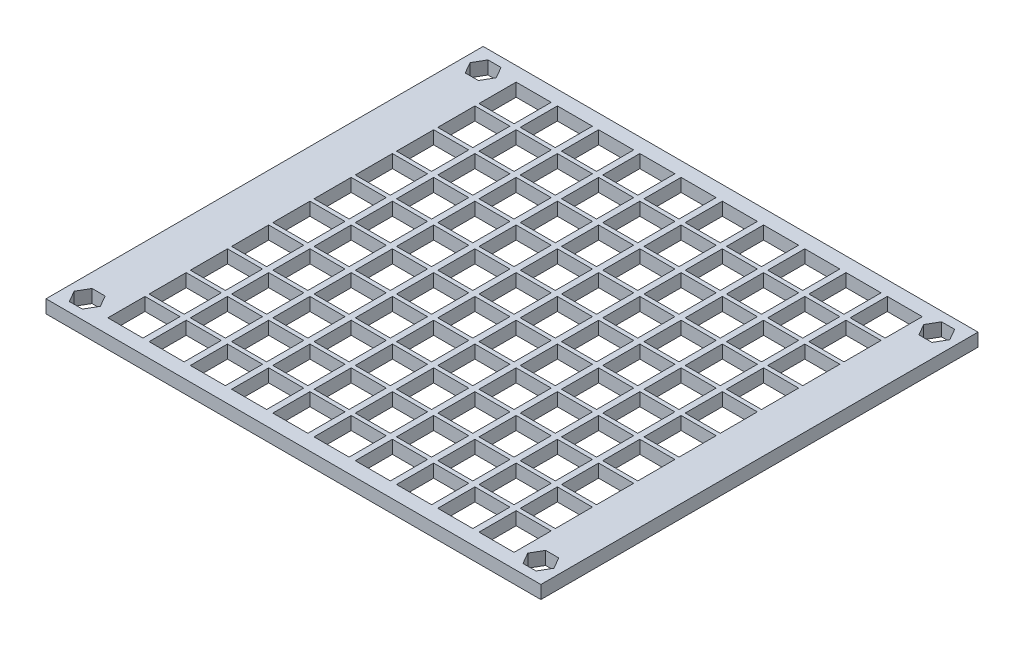
SolidWorks part; units mm, degrees
ref_plane "Front Plane" through (0, 0, 0) normal (0, 0, 1) x (1, 0, 0)
ref_plane "Top Plane" through (0, 0, 0) normal (0, 1, 0) x (1, 0, 0)
ref_plane "Right Plane" through (0, 0, 0) normal (1, 0, 0) x (0, 0, -1)
sketch "Sketch1" plane through (0, 0, 0) normal (0, 1, 0) x (1, 0, 0)
  line L0 (115, 101) -> (5, 101) construction
  line L1 (0, 0) -> (120, 0)
  line L2 (0, 0) -> (0, 106)
  line L3 (0, 106) -> (120, 106)
  line L4 (120, 0) -> (120, 106)
  line L6 (115, 101) -> (115, 5) construction
  line L8 (6.5877, 98.25) -> (8.1754, 101)
  line L9 (8.1754, 101) -> (6.5877, 103.75)
  line L10 (6.5877, 103.75) -> (3.4123, 103.75)
  line L11 (3.4123, 103.75) -> (1.8246, 101)
  line L12 (1.8246, 101) -> (3.4123, 98.25)
  line L13 (3.4123, 98.25) -> (6.5877, 98.25)
  line L14 (21.5, 12.5) -> (21.5, 3.5)
  line L15 (11.5, 12.5) -> (20, 12.5)
  line L16 (11.5, 12.5) -> (11.5, 3.5)
  line L17 (11.5, 3.5) -> (20, 3.5)
  line L18 (20, 12.5) -> (20, 3.5)
  line L19 (21.5, 12.5) -> (30, 12.5)
  line L20 (30, 12.5) -> (30, 3.5)
  line L21 (21.5, 3.5) -> (30, 3.5)
  line L22 (31.5, 12.5) -> (31.5, 3.5)
  line L23 (31.5, 12.5) -> (40, 12.5)
  line L24 (40, 12.5) -> (40, 3.5)
  line L25 (31.5, 3.5) -> (40, 3.5)
  line L26 (41.5, 12.5) -> (41.5, 3.5)
  line L27 (41.5, 12.5) -> (50, 12.5)
  line L28 (50, 12.5) -> (50, 3.5)
  line L29 (41.5, 3.5) -> (50, 3.5)
  line L30 (51.5, 12.5) -> (51.5, 3.5)
  line L31 (51.5, 12.5) -> (60, 12.5)
  line L32 (60, 12.5) -> (60, 3.5)
  line L33 (51.5, 3.5) -> (60, 3.5)
  line L34 (61.5, 12.5) -> (61.5, 3.5)
  line L35 (61.5, 12.5) -> (70, 12.5)
  line L36 (70, 12.5) -> (70, 3.5)
  line L37 (61.5, 3.5) -> (70, 3.5)
  line L38 (71.5, 12.5) -> (71.5, 3.5)
  line L39 (71.5, 12.5) -> (80, 12.5)
  line L40 (80, 12.5) -> (80, 3.5)
  line L41 (71.5, 3.5) -> (80, 3.5)
  line L42 (81.5, 12.5) -> (81.5, 3.5)
  line L43 (81.5, 12.5) -> (90, 12.5)
  line L44 (90, 12.5) -> (90, 3.5)
  line L45 (81.5, 3.5) -> (90, 3.5)
  line L46 (91.5, 12.5) -> (91.5, 3.5)
  line L47 (91.5, 12.5) -> (100, 12.5)
  line L48 (100, 12.5) -> (100, 3.5)
  line L49 (91.5, 3.5) -> (100, 3.5)
  line L50 (101.5, 12.5) -> (101.5, 3.5)
  line L51 (101.5, 12.5) -> (110, 12.5)
  line L52 (110, 12.5) -> (110, 3.5)
  line L53 (101.5, 3.5) -> (110, 3.5)
  line L54 (21.5, 22.5) -> (21.5, 13.5)
  line L55 (21.5, 22.5) -> (30, 22.5)
  line L56 (30, 22.5) -> (30, 13.5)
  line L57 (21.5, 13.5) -> (30, 13.5)
  line L58 (31.5, 22.5) -> (31.5, 13.5)
  line L59 (31.5, 22.5) -> (40, 22.5)
  line L60 (40, 22.5) -> (40, 13.5)
  line L61 (31.5, 13.5) -> (40, 13.5)
  line L62 (41.5, 22.5) -> (41.5, 13.5)
  line L63 (41.5, 22.5) -> (50, 22.5)
  line L64 (50, 22.5) -> (50, 13.5)
  line L65 (41.5, 13.5) -> (50, 13.5)
  line L66 (51.5, 22.5) -> (51.5, 13.5)
  line L67 (51.5, 22.5) -> (60, 22.5)
  line L68 (60, 22.5) -> (60, 13.5)
  line L69 (51.5, 13.5) -> (60, 13.5)
  line L70 (61.5, 22.5) -> (61.5, 13.5)
  line L71 (61.5, 22.5) -> (70, 22.5)
  line L72 (70, 22.5) -> (70, 13.5)
  line L73 (61.5, 13.5) -> (70, 13.5)
  line L74 (71.5, 22.5) -> (71.5, 13.5)
  line L75 (71.5, 22.5) -> (80, 22.5)
  line L76 (80, 22.5) -> (80, 13.5)
  line L77 (71.5, 13.5) -> (80, 13.5)
  line L78 (81.5, 22.5) -> (81.5, 13.5)
  line L79 (81.5, 22.5) -> (90, 22.5)
  line L80 (90, 22.5) -> (90, 13.5)
  line L81 (81.5, 13.5) -> (90, 13.5)
  line L82 (91.5, 22.5) -> (91.5, 13.5)
  line L83 (91.5, 22.5) -> (100, 22.5)
  line L84 (100, 22.5) -> (100, 13.5)
  line L85 (91.5, 13.5) -> (100, 13.5)
  line L86 (101.5, 22.5) -> (101.5, 13.5)
  line L87 (101.5, 22.5) -> (110, 22.5)
  line L88 (110, 22.5) -> (110, 13.5)
  line L89 (101.5, 13.5) -> (110, 13.5)
  line L90 (21.5, 32.5) -> (21.5, 23.5)
  line L91 (21.5, 32.5) -> (30, 32.5)
  line L92 (30, 32.5) -> (30, 23.5)
  line L93 (21.5, 23.5) -> (30, 23.5)
  line L94 (31.5, 32.5) -> (31.5, 23.5)
  line L95 (31.5, 32.5) -> (40, 32.5)
  line L96 (40, 32.5) -> (40, 23.5)
  line L97 (31.5, 23.5) -> (40, 23.5)
  line L98 (41.5, 32.5) -> (41.5, 23.5)
  line L99 (41.5, 32.5) -> (50, 32.5)
  line L100 (50, 32.5) -> (50, 23.5)
  line L101 (41.5, 23.5) -> (50, 23.5)
  line L102 (51.5, 32.5) -> (51.5, 23.5)
  line L103 (51.5, 32.5) -> (60, 32.5)
  line L104 (60, 32.5) -> (60, 23.5)
  line L105 (51.5, 23.5) -> (60, 23.5)
  line L106 (61.5, 32.5) -> (61.5, 23.5)
  line L107 (61.5, 32.5) -> (70, 32.5)
  line L108 (70, 32.5) -> (70, 23.5)
  line L109 (61.5, 23.5) -> (70, 23.5)
  line L110 (71.5, 32.5) -> (71.5, 23.5)
  line L111 (71.5, 32.5) -> (80, 32.5)
  line L112 (80, 32.5) -> (80, 23.5)
  line L113 (71.5, 23.5) -> (80, 23.5)
  line L114 (81.5, 32.5) -> (81.5, 23.5)
  line L115 (81.5, 32.5) -> (90, 32.5)
  line L116 (90, 32.5) -> (90, 23.5)
  line L117 (81.5, 23.5) -> (90, 23.5)
  line L118 (91.5, 32.5) -> (91.5, 23.5)
  line L119 (91.5, 32.5) -> (100, 32.5)
  line L120 (100, 32.5) -> (100, 23.5)
  line L121 (91.5, 23.5) -> (100, 23.5)
  line L122 (101.5, 32.5) -> (101.5, 23.5)
  line L123 (101.5, 32.5) -> (110, 32.5)
  line L124 (110, 32.5) -> (110, 23.5)
  line L125 (101.5, 23.5) -> (110, 23.5)
  line L126 (21.5, 42.5) -> (21.5, 33.5)
  line L127 (21.5, 42.5) -> (30, 42.5)
  line L128 (30, 42.5) -> (30, 33.5)
  line L129 (21.5, 33.5) -> (30, 33.5)
  line L130 (31.5, 42.5) -> (31.5, 33.5)
  line L131 (31.5, 42.5) -> (40, 42.5)
  line L132 (40, 42.5) -> (40, 33.5)
  line L133 (31.5, 33.5) -> (40, 33.5)
  line L134 (41.5, 42.5) -> (41.5, 33.5)
  line L135 (41.5, 42.5) -> (50, 42.5)
  line L136 (50, 42.5) -> (50, 33.5)
  line L137 (41.5, 33.5) -> (50, 33.5)
  line L138 (51.5, 42.5) -> (51.5, 33.5)
  line L139 (51.5, 42.5) -> (60, 42.5)
  line L140 (60, 42.5) -> (60, 33.5)
  line L141 (51.5, 33.5) -> (60, 33.5)
  line L142 (61.5, 42.5) -> (61.5, 33.5)
  line L143 (61.5, 42.5) -> (70, 42.5)
  line L144 (70, 42.5) -> (70, 33.5)
  line L145 (61.5, 33.5) -> (70, 33.5)
  line L146 (71.5, 42.5) -> (71.5, 33.5)
  line L147 (71.5, 42.5) -> (80, 42.5)
  line L148 (80, 42.5) -> (80, 33.5)
  line L149 (71.5, 33.5) -> (80, 33.5)
  line L150 (81.5, 42.5) -> (81.5, 33.5)
  line L151 (81.5, 42.5) -> (90, 42.5)
  line L152 (90, 42.5) -> (90, 33.5)
  line L153 (81.5, 33.5) -> (90, 33.5)
  line L154 (91.5, 42.5) -> (91.5, 33.5)
  line L155 (91.5, 42.5) -> (100, 42.5)
  line L156 (100, 42.5) -> (100, 33.5)
  line L157 (91.5, 33.5) -> (100, 33.5)
  line L158 (101.5, 42.5) -> (101.5, 33.5)
  line L159 (101.5, 42.5) -> (110, 42.5)
  line L160 (110, 42.5) -> (110, 33.5)
  line L161 (101.5, 33.5) -> (110, 33.5)
  line L162 (21.5, 52.5) -> (21.5, 43.5)
  line L163 (21.5, 52.5) -> (30, 52.5)
  line L164 (30, 52.5) -> (30, 43.5)
  line L165 (21.5, 43.5) -> (30, 43.5)
  line L166 (31.5, 52.5) -> (31.5, 43.5)
  line L167 (31.5, 52.5) -> (40, 52.5)
  line L168 (40, 52.5) -> (40, 43.5)
  line L169 (31.5, 43.5) -> (40, 43.5)
  line L170 (41.5, 52.5) -> (41.5, 43.5)
  line L171 (41.5, 52.5) -> (50, 52.5)
  line L172 (50, 52.5) -> (50, 43.5)
  line L173 (41.5, 43.5) -> (50, 43.5)
  line L174 (51.5, 52.5) -> (51.5, 43.5)
  line L175 (51.5, 52.5) -> (60, 52.5)
  line L176 (60, 52.5) -> (60, 43.5)
  line L177 (51.5, 43.5) -> (60, 43.5)
  line L178 (61.5, 52.5) -> (61.5, 43.5)
  line L179 (61.5, 52.5) -> (70, 52.5)
  line L180 (70, 52.5) -> (70, 43.5)
  line L181 (61.5, 43.5) -> (70, 43.5)
  line L182 (71.5, 52.5) -> (71.5, 43.5)
  line L183 (71.5, 52.5) -> (80, 52.5)
  line L184 (80, 52.5) -> (80, 43.5)
  line L185 (71.5, 43.5) -> (80, 43.5)
  line L186 (81.5, 52.5) -> (81.5, 43.5)
  line L187 (81.5, 52.5) -> (90, 52.5)
  line L188 (90, 52.5) -> (90, 43.5)
  line L189 (81.5, 43.5) -> (90, 43.5)
  line L190 (91.5, 52.5) -> (91.5, 43.5)
  line L191 (91.5, 52.5) -> (100, 52.5)
  line L192 (100, 52.5) -> (100, 43.5)
  line L193 (91.5, 43.5) -> (100, 43.5)
  line L194 (101.5, 52.5) -> (101.5, 43.5)
  line L195 (101.5, 52.5) -> (110, 52.5)
  line L196 (110, 52.5) -> (110, 43.5)
  line L197 (101.5, 43.5) -> (110, 43.5)
  line L198 (21.5, 62.5) -> (21.5, 53.5)
  line L199 (21.5, 62.5) -> (30, 62.5)
  line L200 (30, 62.5) -> (30, 53.5)
  line L201 (21.5, 53.5) -> (30, 53.5)
  line L202 (31.5, 62.5) -> (31.5, 53.5)
  line L203 (31.5, 62.5) -> (40, 62.5)
  line L204 (40, 62.5) -> (40, 53.5)
  line L205 (31.5, 53.5) -> (40, 53.5)
  line L206 (41.5, 62.5) -> (41.5, 53.5)
  line L207 (41.5, 62.5) -> (50, 62.5)
  line L208 (50, 62.5) -> (50, 53.5)
  line L209 (41.5, 53.5) -> (50, 53.5)
  line L210 (51.5, 62.5) -> (51.5, 53.5)
  line L211 (51.5, 62.5) -> (60, 62.5)
  line L212 (60, 62.5) -> (60, 53.5)
  line L213 (51.5, 53.5) -> (60, 53.5)
  line L214 (61.5, 62.5) -> (61.5, 53.5)
  line L215 (61.5, 62.5) -> (70, 62.5)
  line L216 (70, 62.5) -> (70, 53.5)
  line L217 (61.5, 53.5) -> (70, 53.5)
  line L218 (71.5, 62.5) -> (71.5, 53.5)
  line L219 (71.5, 62.5) -> (80, 62.5)
  line L220 (80, 62.5) -> (80, 53.5)
  line L221 (71.5, 53.5) -> (80, 53.5)
  line L222 (81.5, 62.5) -> (81.5, 53.5)
  line L223 (81.5, 62.5) -> (90, 62.5)
  line L224 (90, 62.5) -> (90, 53.5)
  line L225 (81.5, 53.5) -> (90, 53.5)
  line L226 (91.5, 62.5) -> (91.5, 53.5)
  line L227 (91.5, 62.5) -> (100, 62.5)
  line L228 (100, 62.5) -> (100, 53.5)
  line L229 (91.5, 53.5) -> (100, 53.5)
  line L230 (101.5, 62.5) -> (101.5, 53.5)
  line L231 (101.5, 62.5) -> (110, 62.5)
  line L232 (110, 62.5) -> (110, 53.5)
  line L233 (101.5, 53.5) -> (110, 53.5)
  line L234 (21.5, 72.5) -> (21.5, 63.5)
  line L235 (21.5, 72.5) -> (30, 72.5)
  line L236 (30, 72.5) -> (30, 63.5)
  line L237 (21.5, 63.5) -> (30, 63.5)
  line L238 (31.5, 72.5) -> (31.5, 63.5)
  line L239 (31.5, 72.5) -> (40, 72.5)
  line L240 (40, 72.5) -> (40, 63.5)
  line L241 (31.5, 63.5) -> (40, 63.5)
  line L242 (41.5, 72.5) -> (41.5, 63.5)
  line L243 (41.5, 72.5) -> (50, 72.5)
  line L244 (50, 72.5) -> (50, 63.5)
  line L245 (41.5, 63.5) -> (50, 63.5)
  line L246 (51.5, 72.5) -> (51.5, 63.5)
  line L247 (51.5, 72.5) -> (60, 72.5)
  line L248 (60, 72.5) -> (60, 63.5)
  line L249 (51.5, 63.5) -> (60, 63.5)
  line L250 (61.5, 72.5) -> (61.5, 63.5)
  line L251 (61.5, 72.5) -> (70, 72.5)
  line L252 (70, 72.5) -> (70, 63.5)
  line L253 (61.5, 63.5) -> (70, 63.5)
  line L254 (71.5, 72.5) -> (71.5, 63.5)
  line L255 (71.5, 72.5) -> (80, 72.5)
  line L256 (80, 72.5) -> (80, 63.5)
  line L257 (71.5, 63.5) -> (80, 63.5)
  line L258 (81.5, 72.5) -> (81.5, 63.5)
  line L259 (81.5, 72.5) -> (90, 72.5)
  line L260 (90, 72.5) -> (90, 63.5)
  line L261 (81.5, 63.5) -> (90, 63.5)
  line L262 (91.5, 72.5) -> (91.5, 63.5)
  line L263 (91.5, 72.5) -> (100, 72.5)
  line L264 (100, 72.5) -> (100, 63.5)
  line L265 (91.5, 63.5) -> (100, 63.5)
  line L266 (101.5, 72.5) -> (101.5, 63.5)
  line L267 (101.5, 72.5) -> (110, 72.5)
  line L268 (110, 72.5) -> (110, 63.5)
  line L269 (101.5, 63.5) -> (110, 63.5)
  line L270 (21.5, 82.5) -> (21.5, 73.5)
  line L271 (21.5, 82.5) -> (30, 82.5)
  line L272 (30, 82.5) -> (30, 73.5)
  line L273 (21.5, 73.5) -> (30, 73.5)
  line L274 (31.5, 82.5) -> (31.5, 73.5)
  line L275 (31.5, 82.5) -> (40, 82.5)
  line L276 (40, 82.5) -> (40, 73.5)
  line L277 (31.5, 73.5) -> (40, 73.5)
  line L278 (41.5, 82.5) -> (41.5, 73.5)
  line L279 (41.5, 82.5) -> (50, 82.5)
  line L280 (50, 82.5) -> (50, 73.5)
  line L281 (41.5, 73.5) -> (50, 73.5)
  line L282 (51.5, 82.5) -> (51.5, 73.5)
  line L283 (51.5, 82.5) -> (60, 82.5)
  line L284 (60, 82.5) -> (60, 73.5)
  line L285 (51.5, 73.5) -> (60, 73.5)
  line L286 (61.5, 82.5) -> (61.5, 73.5)
  line L287 (61.5, 82.5) -> (70, 82.5)
  line L288 (70, 82.5) -> (70, 73.5)
  line L289 (61.5, 73.5) -> (70, 73.5)
  line L290 (71.5, 82.5) -> (71.5, 73.5)
  line L291 (71.5, 82.5) -> (80, 82.5)
  line L292 (80, 82.5) -> (80, 73.5)
  line L293 (71.5, 73.5) -> (80, 73.5)
  line L294 (81.5, 82.5) -> (81.5, 73.5)
  line L295 (81.5, 82.5) -> (90, 82.5)
  line L296 (90, 82.5) -> (90, 73.5)
  line L297 (81.5, 73.5) -> (90, 73.5)
  line L298 (91.5, 82.5) -> (91.5, 73.5)
  line L299 (91.5, 82.5) -> (100, 82.5)
  line L300 (100, 82.5) -> (100, 73.5)
  line L301 (91.5, 73.5) -> (100, 73.5)
  line L302 (101.5, 82.5) -> (101.5, 73.5)
  line L303 (101.5, 82.5) -> (110, 82.5)
  line L304 (110, 82.5) -> (110, 73.5)
  line L305 (101.5, 73.5) -> (110, 73.5)
  line L306 (21.5, 92.5) -> (21.5, 83.5)
  line L307 (21.5, 92.5) -> (30, 92.5)
  line L308 (30, 92.5) -> (30, 83.5)
  line L309 (21.5, 83.5) -> (30, 83.5)
  line L310 (31.5, 92.5) -> (31.5, 83.5)
  line L311 (31.5, 92.5) -> (40, 92.5)
  line L312 (40, 92.5) -> (40, 83.5)
  line L313 (31.5, 83.5) -> (40, 83.5)
  line L314 (41.5, 92.5) -> (41.5, 83.5)
  line L315 (41.5, 92.5) -> (50, 92.5)
  line L316 (50, 92.5) -> (50, 83.5)
  line L317 (41.5, 83.5) -> (50, 83.5)
  line L318 (51.5, 92.5) -> (51.5, 83.5)
  line L319 (51.5, 92.5) -> (60, 92.5)
  line L320 (60, 92.5) -> (60, 83.5)
  line L321 (51.5, 83.5) -> (60, 83.5)
  line L322 (61.5, 92.5) -> (61.5, 83.5)
  line L323 (61.5, 92.5) -> (70, 92.5)
  line L324 (70, 92.5) -> (70, 83.5)
  line L325 (61.5, 83.5) -> (70, 83.5)
  line L326 (71.5, 92.5) -> (71.5, 83.5)
  line L327 (71.5, 92.5) -> (80, 92.5)
  line L328 (80, 92.5) -> (80, 83.5)
  line L329 (71.5, 83.5) -> (80, 83.5)
  line L330 (81.5, 92.5) -> (81.5, 83.5)
  line L331 (81.5, 92.5) -> (90, 92.5)
  line L332 (90, 92.5) -> (90, 83.5)
  line L333 (81.5, 83.5) -> (90, 83.5)
  line L334 (91.5, 92.5) -> (91.5, 83.5)
  line L335 (91.5, 92.5) -> (100, 92.5)
  line L336 (100, 92.5) -> (100, 83.5)
  line L337 (91.5, 83.5) -> (100, 83.5)
  line L338 (101.5, 92.5) -> (101.5, 83.5)
  line L339 (101.5, 92.5) -> (110, 92.5)
  line L340 (110, 92.5) -> (110, 83.5)
  line L341 (101.5, 83.5) -> (110, 83.5)
  line L342 (21.5, 102.5) -> (21.5, 93.5)
  line L343 (21.5, 102.5) -> (30, 102.5)
  line L344 (30, 102.5) -> (30, 93.5)
  line L345 (21.5, 93.5) -> (30, 93.5)
  line L346 (31.5, 102.5) -> (31.5, 93.5)
  line L347 (31.5, 102.5) -> (40, 102.5)
  line L348 (40, 102.5) -> (40, 93.5)
  line L349 (31.5, 93.5) -> (40, 93.5)
  line L350 (41.5, 102.5) -> (41.5, 93.5)
  line L351 (41.5, 102.5) -> (50, 102.5)
  line L352 (50, 102.5) -> (50, 93.5)
  line L353 (41.5, 93.5) -> (50, 93.5)
  line L354 (51.5, 102.5) -> (51.5, 93.5)
  line L355 (51.5, 102.5) -> (60, 102.5)
  line L356 (60, 102.5) -> (60, 93.5)
  line L357 (51.5, 93.5) -> (60, 93.5)
  line L358 (61.5, 102.5) -> (61.5, 93.5)
  line L359 (61.5, 102.5) -> (70, 102.5)
  line L360 (70, 102.5) -> (70, 93.5)
  line L361 (61.5, 93.5) -> (70, 93.5)
  line L362 (71.5, 102.5) -> (71.5, 93.5)
  line L363 (71.5, 102.5) -> (80, 102.5)
  line L364 (80, 102.5) -> (80, 93.5)
  line L365 (71.5, 93.5) -> (80, 93.5)
  line L366 (81.5, 102.5) -> (81.5, 93.5)
  line L367 (81.5, 102.5) -> (90, 102.5)
  line L368 (90, 102.5) -> (90, 93.5)
  line L369 (81.5, 93.5) -> (90, 93.5)
  line L370 (91.5, 102.5) -> (91.5, 93.5)
  line L371 (91.5, 102.5) -> (100, 102.5)
  line L372 (100, 102.5) -> (100, 93.5)
  line L373 (91.5, 93.5) -> (100, 93.5)
  line L374 (101.5, 102.5) -> (101.5, 93.5)
  line L375 (101.5, 102.5) -> (110, 102.5)
  line L376 (110, 102.5) -> (110, 93.5)
  line L377 (101.5, 93.5) -> (110, 93.5)
  line L378 (11.5, 22.5) -> (11.5, 13.5)
  line L379 (11.5, 22.5) -> (20, 22.5)
  line L380 (20, 22.5) -> (20, 13.5)
  line L381 (11.5, 13.5) -> (20, 13.5)
  line L382 (11.5, 32.5) -> (11.5, 23.5)
  line L383 (11.5, 32.5) -> (20, 32.5)
  line L384 (20, 32.5) -> (20, 23.5)
  line L385 (11.5, 23.5) -> (20, 23.5)
  line L386 (11.5, 42.5) -> (11.5, 33.5)
  line L387 (11.5, 42.5) -> (20, 42.5)
  line L388 (20, 42.5) -> (20, 33.5)
  line L389 (11.5, 33.5) -> (20, 33.5)
  line L390 (11.5, 52.5) -> (11.5, 43.5)
  line L391 (11.5, 52.5) -> (20, 52.5)
  line L392 (20, 52.5) -> (20, 43.5)
  line L393 (11.5, 43.5) -> (20, 43.5)
  line L394 (11.5, 62.5) -> (11.5, 53.5)
  line L395 (11.5, 62.5) -> (20, 62.5)
  line L396 (20, 62.5) -> (20, 53.5)
  line L397 (11.5, 53.5) -> (20, 53.5)
  line L398 (11.5, 72.5) -> (11.5, 63.5)
  line L399 (11.5, 72.5) -> (20, 72.5)
  line L400 (20, 72.5) -> (20, 63.5)
  line L401 (11.5, 63.5) -> (20, 63.5)
  line L402 (11.5, 82.5) -> (11.5, 73.5)
  line L403 (11.5, 82.5) -> (20, 82.5)
  line L404 (20, 82.5) -> (20, 73.5)
  line L405 (11.5, 73.5) -> (20, 73.5)
  line L406 (11.5, 92.5) -> (11.5, 83.5)
  line L407 (11.5, 92.5) -> (20, 92.5)
  line L408 (20, 92.5) -> (20, 83.5)
  line L409 (11.5, 83.5) -> (20, 83.5)
  line L410 (11.5, 102.5) -> (11.5, 93.5)
  line L411 (11.5, 102.5) -> (20, 102.5)
  line L412 (20, 102.5) -> (20, 93.5)
  line L413 (11.5, 93.5) -> (20, 93.5)
  line L415 (113.4123, 103.75) -> (111.8246, 101)
  line L416 (111.8246, 101) -> (113.4123, 98.25)
  line L417 (113.4123, 98.25) -> (116.5877, 98.25)
  line L418 (116.5877, 98.25) -> (118.1754, 101)
  line L419 (118.1754, 101) -> (116.5877, 103.75)
  line L420 (116.5877, 103.75) -> (113.4123, 103.75)
  line L421 (113.4123, 7.75) -> (111.8246, 5)
  line L422 (111.8246, 5) -> (113.4123, 2.25)
  line L423 (113.4123, 2.25) -> (116.5877, 2.25)
  line L424 (116.5877, 2.25) -> (118.1754, 5)
  line L425 (118.1754, 5) -> (116.5877, 7.75)
  line L426 (116.5877, 7.75) -> (113.4123, 7.75)
  line L427 (1.8246, 5) -> (3.4123, 2.25)
  line L428 (3.4123, 2.25) -> (6.5877, 2.25)
  line L429 (6.5877, 2.25) -> (8.1754, 5)
  line L430 (8.1754, 5) -> (6.5877, 7.75)
  line L431 (6.5877, 7.75) -> (3.4123, 7.75)
  line L432 (3.4123, 7.75) -> (1.8246, 5)
  circle A28 centre (5, 5) radius 1.7
  circle A29 centre (5, 101) radius 1.7
  circle A30 centre (115, 101) radius 1.7
  circle A31 centre (115, 5) radius 1.7
  circle A129 centre (5, 101) radius 2.75 construction
  circle A130 centre (115, 101) radius 2.75 construction
  circle A131 centre (115, 5) radius 2.75 construction
  circle A132 centre (5, 5) radius 2.75 construction
  point P7 (115, 53)
  point P9 (60, 101)
  point P10 (60, 106)
  point P20 (120, 53)
  point P25 (0, 0)
  point P31 (0, 0)
  point P441 (0, 0)
  dimension "D5" = 110
  dimension "D6" = 96
  dimension "D3" = 9
  dimension "D8" = 3.4
  dimension "D1" = 120
  dimension "D2" = 106
  dimension "D4" = 8.5
  dimension "D7" = 10
  dimension "D10" = 6.5
  dimension "D11" = 1.5
  dimension "D12" = 5.5
  dimension "D9" = 10
extrude "Boss-Extrude1" add sketch "Sketch1" along normal blind 3.175
equation "\"o\"= 10mm"
equation "\"P\"= 10"
